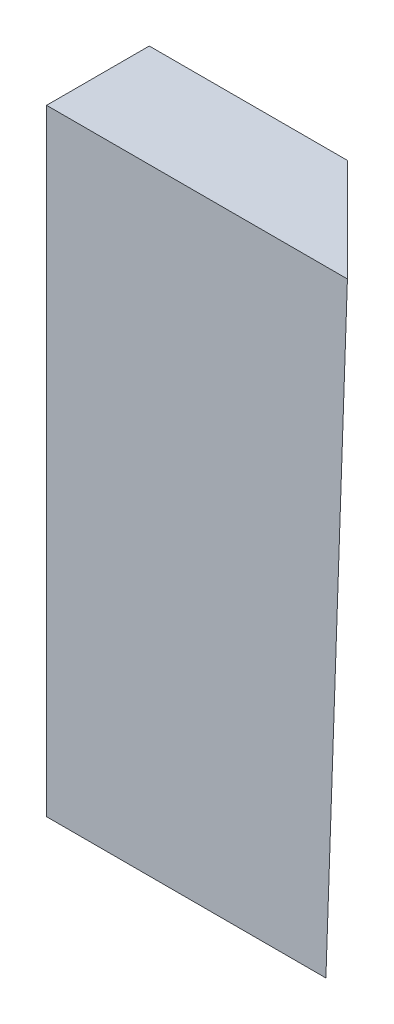
SolidWorks part; units mm, degrees
ref_plane "Alzado" through (0, 0, 0) normal (0, 0, 1) x (1, 0, 0)
ref_plane "Planta" through (0, 0, 0) normal (0, 1, 0) x (1, 0, 0)
ref_plane "Vista lateral" through (0, 0, 0) normal (1, 0, 0) x (0, 0, -1)
sketch "Croquis1" plane through (0, 0, 0) normal (0, 1, 0) x (1, 0, 0)
  line L0 (0, 0) -> (34, 0)
  line L1 (34, 0) -> (21.5, 12.5)
  line L2 (21.5, 12.5) -> (0, 12.5)
  line L3 (0, 12.5) -> (0, 0)
  point P3 (26.609, 10.0808)
  dimension "D1" = 34
  dimension "D2" = 21.5
  dimension "D3" = 12.5
ref_plane "Plano1" through (0, 75, 0) normal (0, -1, 0) x (-1, 0, 0)
sketch "Croquis2" plane through (0, 75, 0) normal (0, -1, 0) x (-1, 0, 0)
  line L1 (-36.62, 0) -> (-24.12, 12.5)
  line L2 (-36.62, 0) -> (0, 0)
  line L3 (0, 0) -> (0, 12.5)
  line L4 (0, 12.5) -> (-24.12, 12.5)
  point P2 (0, 0)
  dimension "D1" = 36.62
  dimension "D2" = 24.12
  dimension "D3" = 12.5
loft "Recubrir1" add profiles "Croquis2", "Croquis1"
